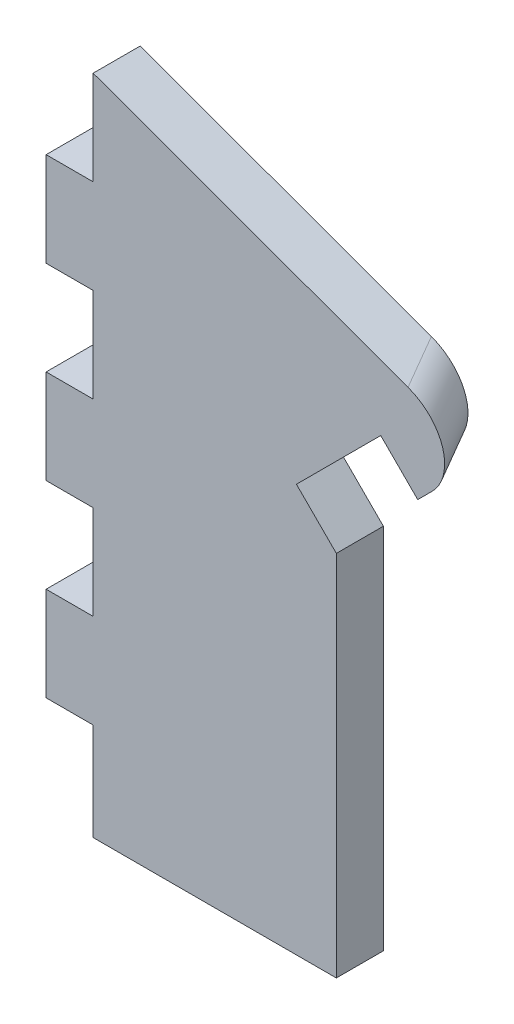
SolidWorks part; units mm, degrees
ref_plane "Front Plane" through (0, 0, 0) normal (0, 0, 1) x (1, 0, 0)
ref_plane "Top Plane" through (0, 0, 0) normal (0, 1, 0) x (1, 0, 0)
ref_plane "Right Plane" through (0, 0, 0) normal (1, 0, 0) x (0, 0, -1)
sketch "Sketch1" plane through (0, 0, 0) normal (0, 0, 1) x (1, 0, 0)
  line L1 (0, 0) -> (119.1443, 0)
  line L2 (0, 0) -> (0, 140.7246)
  line L3 (0, 140.7246) -> (119.1443, 140.7246)
  line L4 (119.1443, 0) -> (119.1443, 140.7246)
extrude "Boss-Extrude1" add sketch "Sketch1" along normal blind 10
sketch "Sketch2" plane through (0, 0, 10) normal (0, 0, 1) x (1, 0, 0)
  line L0 (10, 140.7246) -> (10, 0) construction
  line L1 (119.1443, 140.7246) -> (0, 140.7246) construction
  line L2 (0, 0) -> (119.1443, 0) construction
  line L3 (0, 140.7246) -> (0, 0) construction
  line L4 (0, 40.7246) -> (10, 40.7246)
  line L5 (10, 40.7246) -> (10, 60.7246)
  line L6 (10, 60.7246) -> (0, 60.7246)
  line L7 (0, 20.7246) -> (10, 20.7246)
  line L8 (0, 80.7246) -> (10, 80.7246)
  line L9 (10, 80.7246) -> (10, 100.7246)
  line L10 (10, 100.7246) -> (0, 100.7246)
  line L11 (0, 100.7246) -> (0, 80.7246)
  line L12 (0, 120.7246) -> (10, 120.7246)
  line L13 (10, 120.7246) -> (10, 140.7246)
  line L14 (10, 140.7246) -> (0, 140.7246)
  line L15 (0, 60.7246) -> (0, 40.7246)
  line L16 (0, 100.7246) -> (0, 80.7246)
  line L17 (0, 140.7246) -> (0, 120.7246)
  line L18 (0, 60.7246) -> (0, 40.7246)
  line L19 (10, 20.7246) -> (10, 0)
  line L20 (10, 0) -> (0, 0)
  line L21 (0, 0) -> (0, 20.7246)
  line M1 (0, 140.7246) -> (0, 0)
  line M2 (0, 0) -> (119.1443, 0)
  dimension "D1" = 10
  dimension "D2" = 20
  dimension "D3" = 20
  dimension "D4" = 20
  dimension "D5" = 20
  dimension "D6" = 20
  dimension "D7" = 20
extrude "Cut-Extrude1" cut sketch "Sketch2" against normal blind 10 contours L5 L6 L4 M1 | L9 L10 L8 M1 | L19 L7 M1 M2 | L17 L12 L13 L14
sketch "Sketch4" plane through (0, 0, 10) normal (0, 0, 1) x (1, 0, 0)
  line L0 (10, 140.7246) -> (119.1443, 100.9993)
  line L2 (119.1443, 0) -> (119.1443, 140.7246) construction
  line L3 (119.1443, 100.9993) -> (119.1443, 140.7246)
  line L4 (119.1443, 140.7246) -> (10, 140.7246)
  line L5 (10, 120.7246) -> (10, 140.7246) construction
  dimension "D1" = 70
extrude "Cut-Extrude2" cut sketch "Sketch4" against normal blind 10
sketch "Sketch5" plane through (-16.2997, 16.2957, 11.2094) normal (-0.636, 0.6358, 0.4374) x (0.3093, -0.3092, 0.8993)
  line L0 (-35.2099, 111.3393) -> (18.6725, 122.3249)
  line L1 (18.6725, 122.3249) -> (22.6679, 102.728)
  line L2 (22.6679, 102.728) -> (-31.2145, 91.7425)
  line L3 (-31.2145, 91.7425) -> (-35.2099, 111.3393)
  line L5 (-12.4648, 136.3881) -> (-1.3448, 138.6552)
  line L6 (-12.4648, 136.3881) -> (-1.3448, 138.6552) construction
  dimension "D2" = 20
sketch "Sketch7" plane through (0, 0, 10) normal (0, 0, 1) x (1, 0, 0)
  line L0 (76.128, 92.6052) -> (93.7578, 110.2393)
  line L2 (10, 140.7246) -> (119.1443, 100.9993) construction
  line L5 (61.6967, 78.1703) -> (61.6967, 0)
  line L7 (10, 0) -> (119.1443, 0) construction
  line L8 (10, 40.7246) -> (10, 60.7246) construction
  line L9 (61.6967, 78.1703) -> (76.128, 92.6052)
  line L10 (93.7578, 110.2393) -> (119.1443, 100.9993)
  line L11 (119.1443, 100.9993) -> (119.1443, 0)
  line L12 (119.1443, 0) -> (61.6967, 0)
  line L13 (35.1432, 68.583) -> (81.4448, 114.8959)
  line L14 (35.1432, 68.583) -> (81.4448, 114.8959) construction
  dimension "D1" = 12
  dimension "D2" = 12
extrude "Cut-Extrude6" cut sketch "Sketch7" against normal blind 150
sketch "Sketch9" plane through (-8.2293, 8.2273, 0) normal (0.7072, -0.707, 0) x (0, 0, -1)
  line L0 (0, 98.9023) -> (0, 144.2491) construction
  line L1 (-10, 98.9023) -> (0, 98.9023)
  line L2 (-10, 98.9023) -> (-10, 124.2491)
  line L3 (-10, 124.2491) -> (0, 124.2491)
  line L4 (0, 98.9023) -> (0, 124.2491)
  line L5 (-10, 144.2491) -> (0, 144.2491) construction
  dimension "D1" = 20
extrude "Cut-Extrude7" cut sketch "Sketch9" against normal up to surface (12 mm away)
sketch "Sketch10" plane through (-9.94, 9.9376, 6.8358) normal (0.636, -0.6358, -0.4374) x (-0.3093, 0.3092, -0.8993)
  line L1 (-12.1481, 149.1727) -> (18.8926, 149.1727)
  line L2 (-12.1481, 149.1727) -> (-12.1481, 117.5525)
  line L3 (-12.1481, 117.5525) -> (18.8926, 117.5525)
  line L4 (18.8926, 149.1727) -> (18.8926, 117.5525)
extrude "Cut-Extrude8" cut sketch "Sketch10" along normal blind 150
fillet "Fillet1" radius 10 1 edges at (90.3242, 111.489, 5)
